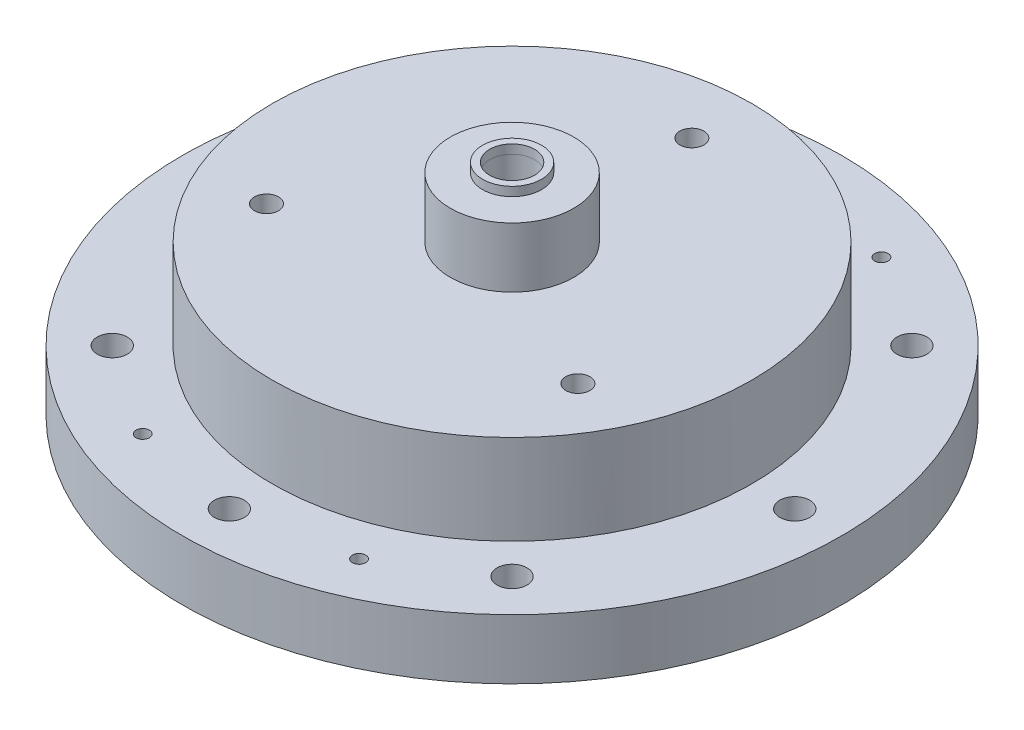
SolidWorks part; units mm, degrees
ref_plane "Front Plane" through (0, 0, 0) normal (0, 0, 1) x (1, 0, 0)
ref_plane "Top Plane" through (0, 0, 0) normal (0, 1, 0) x (1, 0, 0)
ref_plane "Right Plane" through (0, 0, 0) normal (1, 0, 0) x (0, 0, -1)
sketch "Sketch1" plane through (0, 0, 0) normal (0, 1, 0) x (1, 0, 0)
  circle A1 centre (0, 0) radius 50.8
  dimension "D1" = 101.6
extrude "Boss-Extrude1" add sketch "Sketch1" along normal blind 25.4
sketch "Sketch2" plane through (0, 0, 0) normal (0, -1, 0) x (1, 0, 0)
  circle A0 centre (0, 0) radius 50.8
  circle A1 centre (0, 0) radius 69.85
  dimension "D1" = 139.7
extrude "Boss-Extrude2" add sketch "Sketch2" against normal blind 12.7
sketch "Sketch4" plane through (0, 0, 0) normal (0, -1, 0) x (1, 0, 0)
  circle A0 centre (0, -59.9186) radius 3.175
  circle A1 centre (-42.3688, -42.3688) radius 3.175
  circle A2 centre (-59.9186, 0) radius 3.175
  circle A3 centre (-42.3688, 42.3688) radius 3.175
  circle A4 centre (0, 59.9186) radius 3.175
  circle A5 centre (42.3688, 42.3688) radius 3.175
  circle A6 centre (59.9186, 0) radius 3.175
  circle A7 centre (42.3688, -42.3688) radius 3.175
  point P35 (0, 0)
  dimension "D2" = 6.35
  dimension "D1" = 59.9186
  dimension "D3" = 8
extrude "Cut-Extrude2" cut sketch "Sketch4" against normal up to next
sketch "Sketch5" plane through (0, 25.4, 0) normal (0, 1, 0) x (1, 0, 0)
  circle A0 centre (0, 0) radius 12.827
  dimension "D1" = 25.654
extrude "Cut-Extrude3" cut sketch "Sketch5" against normal blind 19.05 from offset 0
sketch "Sketch6" plane through (0, 6.35, 0) normal (0, 1, 0) x (1, 0, 0)
  circle A0 centre (0, 0) radius 1.5875
  dimension "D1" = 3.175
extrude "Cut-Extrude4" cut sketch "Sketch6" against normal up to next
sketch "Sketch34" plane through (0, 25.4, 0) normal (0, 1, 0) x (1, 0, 0)
  circle A0 centre (0, 0) radius 13.081
  circle A1 centre (0, 0) radius 4.7625
  dimension "D1" = 26.162
  dimension "D2" = 9.525
extrude "Boss-Extrude3" add sketch "Sketch34" along normal blind 19.05
cosmetic thread "Cosmetic Thread4" parameters "D2"=23.1953
sketch "Sketch40" plane through (0, 25.4, 0) normal (0, 1, 0) x (1, 0, 0)
  circle A0 centre (0, 0) radius 50.8
extrude "Boss-Extrude5" add sketch "Sketch40" along normal blind 6.35
sketch "Sketch38" plane through (0, 44.45, 0) normal (0, 1, 0) x (1, 0, 0)
  circle A0 centre (0, 0) radius 6.2484
  dimension "D1" = 12.4968
extrude "Boss-Extrude4" add sketch "Sketch38" along normal blind 1.905 separate body
sketch "Sketch39" plane through (0, 46.355, 0) normal (0, 1, 0) x (1, 0, 0)
  circle A0 centre (0, 0) radius 4.7625
  dimension "D1" = 9.525
extrude "Cut-Extrude7" cut sketch "Sketch39" against normal blind 6.35
sketch "Sketch41" plane through (0, 31.75, 0) normal (0, 1, 0) x (1, 0, 0)
  circle A0 centre (0, 0) radius 4.7625
  dimension "D1" = 9.525
extrude "Cut-Extrude8" cut sketch "Sketch41" against normal blind 6.35
sketch "Sketch42" plane through (0, 0, 0) normal (0, -1, 0) x (1, 0, 0)
  circle A0 centre (0, 0) radius 23.7871
  dimension "D1" = 47.5742
extrude "Cut-Extrude9" cut sketch "Sketch42" against normal blind 6.477
hole_wizard "#10-24 Tapped Hole1" positions "Sketch44" profile "Sketch45" tap size "#10-24" standard "ANSI Inch"
sketch "Sketch44" plane through (0, 6.477, 0) normal (0, -1, 0) x (-1, 0, 0)
  line L0 (0, 0) -> (0, -35.56) construction
  line L2 (0, 0) -> (0, 30.48) construction
  line L4 (0, 0) -> (-27.94, 0) construction
  line L6 (0, 0) -> (30.48, 0) construction
  circle A0 centre (0, 0) radius 17.4625 construction
  point P0 (0, -17.4625)
  point P2 (-17.4625, 0)
  point P4 (0, 17.4625)
  point P6 (17.4625, 0)
  dimension "D1" = 34.925
sketch "Sketch45" plane through (0, 6.477, 17.4625) normal (1, 0, 0) x (0, 0, -1)
  line L0 (0, 0) -> (0, 13.8408)
  line L1 (0, 13.8408) -> (1.8986, 12.7)
  line L2 (1.8986, 12.7) -> (1.8986, 0)
  line L5 (1.8986, 0) -> (0, 0)
  line L10 (0, 13.8408) -> (-1.8987, 12.7) construction
  line L11 (0, -6.35) -> (0, 107.95) construction
  dimension "Tap Drill Dia." = 3.7973
  dimension "Tap Drill Depth" = 12.7
  dimension "Drill Angle" = 118
cosmetic thread "Hole Thread1" parameters "D1"=9.652, "D2"=4.826
cosmetic thread "Hole Thread2" parameters "D1"=9.652, "D2"=4.826
cosmetic thread "Hole Thread3" parameters "D1"=9.652, "D2"=4.826
cosmetic thread "Hole Thread4" parameters "D1"=9.652, "D2"=4.826
sketch "Sketch46" plane through (0, 0, 0) normal (0, -1, 0) x (1, 0, 0)
  line L0 (0, -83.82) -> (0, 83.82) construction
  line L1 (34.3522, -82.9336) -> (-34.3522, 82.9336) construction
  line L2 (-32.8909, -79.4057) -> (32.8909, 79.4057) construction
  circle A0 centre (0, 0) radius 59.9186 construction
  circle A1 centre (-22.9299, 55.3576) radius 3.175
  circle A2 centre (22.9299, 55.3576) radius 3.175
  circle A3 centre (-22.9299, -55.3576) radius 3.175
  circle A4 centre (22.9299, -55.3576) radius 3.175
  point P7 (0, 0)
  point P10 (0, 0)
  point P12 (0, 0)
  dimension "D1" = 119.8372
  dimension "D4" = 6.35
  dimension "D5" = 6.35
  dimension "D6" = 6.35
  dimension "D7" = 6.35
  dimension "D2" = 22.5
  dimension "D3" = 22.5
extrude "Cut-Extrude10" cut sketch "Sketch46" against normal blind 6.35
hole_wizard "1/4-20 Tapped Hole1" positions "Sketch47" profile "Sketch48" tap size "1/4-20" standard "ANSI Inch"
sketch "Sketch47" plane through (0, 31.75, 0) normal (0, 1, 0) x (1, 0, 0)
  line L0 (0, 0) -> (0, 45.3569) construction
  line L2 (0, 0) -> (-40.0078, -23.0985) construction
  line L4 (0, 0) -> (38.662, -22.3215) construction
  circle A0 centre (0, 0) radius 38.1 construction
  point P0 (0, 38.1)
  point P2 (32.9956, -19.05)
  point P4 (-32.9956, -19.05)
  dimension "D1" = 76.2
  dimension "D2" = 120
  dimension "D3" = 120
sketch "Sketch48" plane through (0, 31.75, -38.1) normal (1, 0, 0) x (0, 0, 1)
  line L0 (0, 0) -> (0, 15.5038)
  line L1 (0, 15.5038) -> (2.5527, 13.97)
  line L2 (2.5527, 13.97) -> (2.5527, 0)
  line L5 (2.5527, 0) -> (0, 0)
  line L10 (0, 15.5038) -> (-2.5527, 13.97) construction
  line L11 (0, -6.35) -> (0, 107.95) construction
  dimension "Tap Drill Dia." = 5.1054
  dimension "Tap Drill Depth" = 13.97
  dimension "Drill Angle" = 118
cosmetic thread "Hole Thread5" parameters "D1"=12.7, "D2"=6.35
cosmetic thread "Hole Thread6" parameters "D1"=12.7, "D2"=6.35
cosmetic thread "Hole Thread7" parameters "D1"=12.7, "D2"=6.35
sketch "Sketch49" plane through (0, 6.477, 0) normal (0, -1, 0) x (1, 0, 0)
  circle A0 centre (0, 0) radius 23.8252
  dimension "D1" = 47.6504
extrude "Cut-Extrude11" cut sketch "Sketch49" against normal blind 3.937 from surface at 6.477 starting at face at (22.9299, 0, 52.1826)
sketch "Sketch50" plane through (0, 6.35, 0) normal (0, -1, 0) x (1, 0, 0)
  circle A0 centre (-22.9299, 55.3576) radius 1.4097
  circle A1 centre (22.9299, 55.3576) radius 1.4097
  circle A2 centre (-22.9299, -55.3576) radius 1.4097
  circle A3 centre (22.9299, -55.3576) radius 1.4097
  dimension "D1" = 2.8194
  dimension "D2" = 2.8194
  dimension "D3" = 2.8194
  dimension "D4" = 2.8194
extrude "Cut-Extrude12" cut sketch "Sketch50" against normal through all
